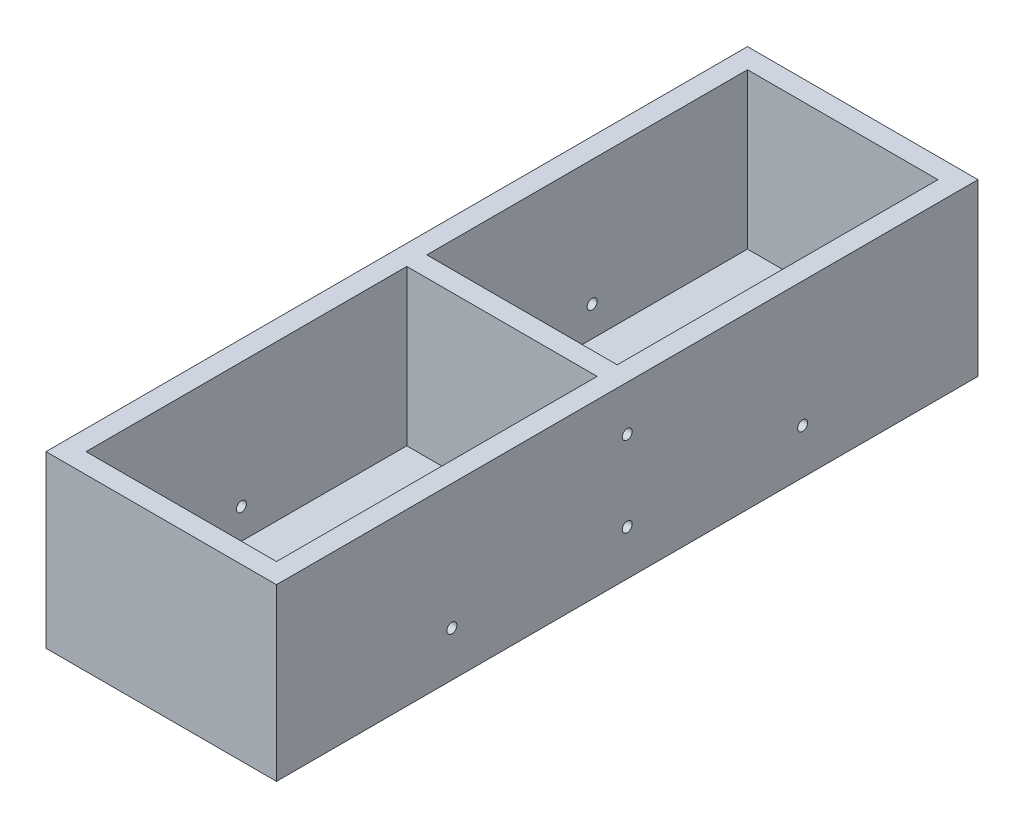
SolidWorks part; units mm, degrees
ref_plane "Front Plane" through (0, 0, 0) normal (0, 0, 1) x (1, 0, 0)
ref_plane "Top Plane" through (0, 0, 0) normal (0, 1, 0) x (1, 0, 0)
ref_plane "Right Plane" through (0, 0, 0) normal (1, 0, 0) x (0, 0, -1)
sketch "Sketch1" plane through (0, 0, 0) normal (0, 0, 1) x (1, 0, 0)
  line L0 (0, 8.5) -> (0, -8.5) construction
  line L1 (-11.5, -8.5) -> (11.5, -8.5)
  line L2 (-11.5, -8.5) -> (-11.5, 8.5)
  line L3 (-11.5, 8.5) -> (11.5, 8.5)
  line L4 (11.5, -8.5) -> (11.5, 8.5)
  line L5 (-11.5, -8.5) -> (11.5, 8.5) construction
  line L6 (-11.5, 8.5) -> (11.5, -8.5) construction
  line L7 (9.4706, 7) -> (9.5, 7)
  line L8 (-9.5, -7) -> (9.5, -7)
  line L9 (-9.5, -7) -> (-9.5, 7)
  line L10 (-9.5, 7) -> (-9.4706, 7)
  line L11 (9.5, -7) -> (9.5, 7)
  line L12 (-9.5, -7) -> (9.5, 7) construction
  line L13 (-9.5, 7) -> (9.5, -7) construction
  line L14 (-9.5, 7) -> (-9.4706, 7)
  line L15 (-9.5, 7) -> (-9.5, 8.5)
  line L16 (-9.5, 8.5) -> (9.5, 8.5)
  line L17 (9.5, 7) -> (9.5, 8.5)
  line L18 (9.4706, 7) -> (9.5, 7)
  line L19 (-9.5, 8.5) -> (-9.5, -7)
  line L20 (-9.5, -7) -> (9.5, -7)
  line L21 (9.5, -7) -> (9.5, 8.5)
  line L22 (-9.5, 8.5) -> (9.5, 8.5)
  point P0 (0, 0)
  point P8 (0, 0)
  dimension "D1" = 23
  dimension "D2" = 17
  dimension "D3" = 19
  dimension "D4" = 14
extrude "Boss-Extrude1" add sketch "Sketch1" along normal blind 70 contours L17 L11 L8 L9 L15 L3 L2 L1 L4
sketch "Sketch2" plane through (0, 0, 70) normal (0, 0, 1) x (1, 0, 0)
  line L1 (-11.5, -8.5) -> (11.5, -8.5)
  line L2 (-11.5, -8.5) -> (-11.5, 8.5)
  line L3 (-11.5, 8.5) -> (11.5, 8.5)
  line L4 (11.5, -8.5) -> (11.5, 8.5)
  line L5 (-11.5, -8.5) -> (11.5, 8.5) construction
  line L6 (-11.5, 8.5) -> (11.5, -8.5) construction
  point P0 (0, 0)
extrude "Boss-Extrude2" add sketch "Sketch2" against normal blind 2
sketch "Sketch3" plane through (0, 0, 0) normal (0, 0, -1) x (-1, 0, 0)
  line L1 (-11.5, -8.5) -> (11.5, -8.5)
  line L2 (-11.5, -8.5) -> (-11.5, 8.5)
  line L3 (-11.5, 8.5) -> (11.5, 8.5)
  line L4 (11.5, -8.5) -> (11.5, 8.5)
  line L5 (-11.5, -8.5) -> (11.5, 8.5) construction
  line L6 (-11.5, 8.5) -> (11.5, -8.5) construction
  point P0 (0, 0)
extrude "Boss-Extrude3" add sketch "Sketch3" against normal blind 2
ref_plane "Plane1" through (0, 0, 35) normal (0, 0, -1) x (-1, 0, 0)
sketch "Sketch4" plane through (0, 0, 35) normal (0, 0, -1) x (-1, 0, 0)
  line L1 (-11.5, -8.5) -> (11.5, -8.5)
  line L2 (-11.5, -8.5) -> (-11.5, 8.5)
  line L3 (-11.5, 8.5) -> (11.5, 8.5)
  line L4 (11.5, -8.5) -> (11.5, 8.5)
  line L5 (-11.5, -8.5) -> (11.5, 8.5) construction
  line L6 (-11.5, 8.5) -> (11.5, -8.5) construction
  point P0 (0, 0)
extrude "Boss-Extrude4" add sketch "Sketch4" along normal blind 1 and the other way blind 1
sketch "Sketch6" plane through (11.5, 0, 0) normal (1, 0, 0) x (0, 0, -1)
  line L0 (-35, -8.5) -> (-35, -4) construction
  line L3 (-70, -8.5) -> (0, -8.5) construction
  circle A0 centre (-35, -4) radius 0.5
extrude "Cut-Extrude7" cut sketch "Sketch6" against normal blind 57
sketch "Sketch7" plane through (11.5, 0, 0) normal (1, 0, 0) x (0, 0, -1)
  line L0 (-70, -8.5) -> (-35, -8.5) construction
  line L1 (-70, -8.5) -> (0, -8.5) construction
  line L2 (-52.5, -8.5) -> (-52.5, -4) construction
  circle A0 centre (-52.5, -4) radius 0.5
extrude "Cut-Extrude8" cut sketch "Sketch7" against normal blind 57
mirror "Mirror1" about plane through (0, 0, 35) normal (0, 0, -1) of "Cut-Extrude8"
mirror "Mirror2" about plane through (0, 0, 0) normal (0, 1, 0) of "Cut-Extrude7"
